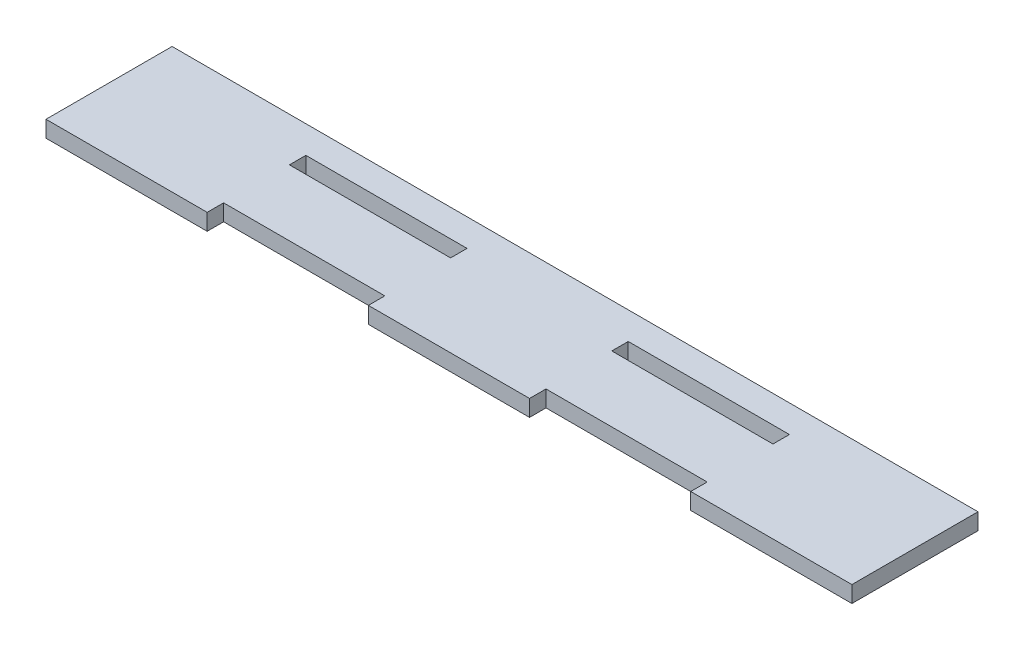
SolidWorks part; units mm, degrees
ref_plane "Front Plane" through (0, 0, 0) normal (0, 0, 1) x (1, 0, 0)
ref_plane "Top Plane" through (0, 0, 0) normal (0, 1, 0) x (1, 0, 0)
ref_plane "Right Plane" through (0, 0, 0) normal (1, 0, 0) x (0, 0, -1)
sketch "Sketch1" plane through (0, 0, 0) normal (0, 1, 0) x (1, 0, 0)
  line L0 (14.7, -0.5) -> (44.1, -0.5)
  line L1 (-73.5, 7.5) -> (73.5, 7.5)
  line L2 (-73.5, 7.5) -> (-73.5, -15.5)
  line L3 (-73.5, -15.5) -> (-44.1, -15.5)
  line L4 (73.5, 7.5) -> (73.5, -15.5)
  line L5 (-44.1, 2.5) -> (-14.7, 2.5)
  line L6 (-44.1, -12.5) -> (-14.7, -12.5)
  line L7 (-44.1, -0.5) -> (-14.7, -0.5)
  line L8 (14.7, 2.5) -> (44.1, 2.5)
  line L9 (-44.1, -12.5) -> (-44.1, -15.5)
  line L10 (-44.1, 2.5) -> (-44.1, -0.5)
  line L11 (-14.7, 2.5) -> (-14.7, -0.5)
  line L12 (14.7, 2.5) -> (14.7, -0.5)
  line L13 (44.1, 2.5) -> (44.1, -0.5)
  line L14 (-14.7, -12.5) -> (-14.7, -15.5)
  line L15 (14.7, -12.5) -> (14.7, -15.5)
  line L16 (44.1, -12.5) -> (44.1, -15.5)
  line L17 (-14.7, -15.5) -> (14.7, -15.5)
  line L18 (44.1, -15.5) -> (73.5, -15.5)
  line L19 (14.7, -12.5) -> (44.1, -12.5)
  point P0 (0, 0)
  dimension "D1" = 23
  dimension "D2" = 147
  dimension "D3" = 12
  dimension "D4" = 3
extrude "Boss-Extrude1" add sketch "Sketch1" along normal blind 3
